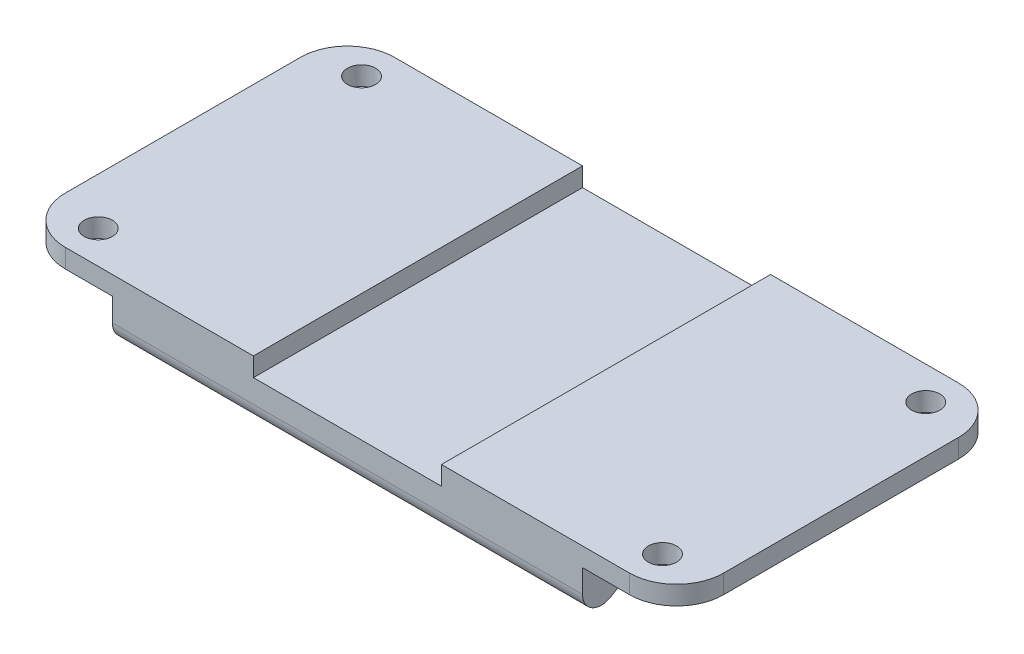
SolidWorks part; units mm, degrees
material "PEI"
ref_plane "Front Plane" through (0, 0, 0) normal (0, 0, 1) x (1, 0, 0)
ref_plane "Top Plane" through (0, 0, 0) normal (0, 1, 0) x (1, 0, 0)
ref_plane "Right Plane" through (0, 0, 0) normal (1, 0, 0) x (0, 0, -1)
sketch "Sketch1" plane through (0, 0, 0) normal (0, 1, 0) x (1, 0, 0)
  line L1 (25, -17.5) -> (-25, -17.5)
  line L2 (25, -17.5) -> (25, 17.5)
  line L3 (25, 17.5) -> (-25, 17.5)
  line L4 (-25, -17.5) -> (-25, 17.5)
  line L5 (25, -17.5) -> (-25, 17.5) construction
  line L6 (25, 17.5) -> (-25, -17.5) construction
  point P0 (0, 0)
  dimension "D1" = 35
  dimension "D2" = 50
extrude "Boss-Extrude1" add sketch "Sketch1" against normal blind 8
sketch "Sketch2" plane through (25, 0, 0) normal (1, 0, 0) x (0, 0, -1)
  line L0 (-17.5, -8) -> (-12.5, -5)
  line L1 (-12.5, -5) -> (12.5, -5)
  line L2 (0, -5) -> (0, -8)
  line L3 (17.5, -8) -> (12.5, -5)
  line L4 (17.5, 0) -> (-17.5, 0)
  line L5 (-17.5, 0) -> (-17.5, -8)
  line L6 (-17.5, -8) -> (17.5, -8)
  line L7 (17.5, -8) -> (17.5, 0)
  line L8 (17.5, 0) -> (-17.5, 0)
  line L9 (-17.5, 0) -> (-17.5, -8)
  line L10 (-17.5, -8) -> (17.5, -8)
  line L11 (17.5, -8) -> (17.5, 0)
  line M7 (-17.5, -8) -> (17.5, -8)
  dimension "D2" = 5
  dimension "D3" = 3
  dimension "D1" = 0
extrude "Cut-Extrude1" cut sketch "Sketch2" against normal through all and the other way through all contours L2 L1 L0 M7 | L3 L1 L2 M7
fillet "Fillet1" radius 2 4 edges at (0, -5, 12.5) (0, -5, -12.5) (0, -8, -17.5) (0, -8, 17.5)
sketch "Sketch3" plane through (0, 0, 17.5) normal (0, 0, 1) x (1, 0, 0)
  line L0 (-25, 0) -> (25, 0) construction
  line L1 (-10, 2) -> (10, 2)
  line L2 (-10, 2) -> (-10, -2)
  line L3 (-10, -2) -> (10, -2)
  line L4 (-25, 0) -> (-25, -4.4676)
  line L5 (-25, -4.4676) -> (25, -4.4676)
  line L6 (25, -4.4676) -> (25, 0)
  line L7 (25, 0) -> (-25, 0)
  line L8 (-25, 0) -> (-25, -4.4676)
  line L9 (-25, -4.4676) -> (25, -4.4676)
  line L10 (25, -4.4676) -> (25, 0)
  line L11 (25, 0) -> (-25, 0)
  line L12 (10, 2) -> (10, -2)
  line L13 (-10, 2) -> (10, -2) construction
  line L14 (-10, -2) -> (10, 2) construction
  line L15 (0, 0) -> (0, -4.4676)
  point P2 (0, 0)
  point P18 (0, 0)
  line M10 (25, 0) -> (-25, 0)
  dimension "D2" = 20
  dimension "D3" = 4
  dimension "D1" = 0
sketch "Sketch5" plane through (-25, 0, 0) normal (-1, 0, 0) x (0, 0, 1)
  line L1 (-17.5, 0) -> (17.5, 0)
  line L2 (-17.5, 0) -> (-17.5, -2)
  line L3 (-17.5, -2) -> (17.5, -2)
  line L4 (17.5, 0) -> (17.5, -2)
  line L6 (-17.5, 0) -> (-17.5, -4.4676)
  line L7 (-14.471, -6.1826) -> (-12.975, -5.285)
  line L8 (-11.946, -5) -> (11.946, -5)
  line L9 (12.975, -5.285) -> (14.471, -6.1826)
  line L10 (17.5, -4.4676) -> (17.5, 0)
  line L11 (17.5, 0) -> (-17.5, 0)
  line L12 (-17.5, 0) -> (-17.5, -4.4676)
  line L13 (-14.471, -6.1826) -> (-12.975, -5.285)
  line L14 (-11.946, -5) -> (11.946, -5)
  line L15 (12.975, -5.285) -> (14.471, -6.1826)
  line L16 (17.5, -4.4676) -> (17.5, 0)
  line L17 (17.5, 0) -> (-17.5, 0)
  arc A4 (-17.5, -4.4676) -> (-14.471, -6.1826) centre (-15.5, -4.4676) ccw
  arc A5 (-11.946, -5) -> (-12.975, -5.285) centre (-11.946, -7) ccw
  arc A6 (12.975, -5.285) -> (11.946, -5) centre (11.946, -7) ccw
  arc A7 (14.471, -6.1826) -> (17.5, -4.4676) centre (15.5, -4.4676) ccw
  arc A8 (-17.5, -4.4676) -> (-14.471, -6.1826) centre (-15.5, -4.4676) ccw
  arc A9 (-11.946, -5) -> (-12.975, -5.285) centre (-11.946, -7) ccw
  arc A10 (12.975, -5.285) -> (11.946, -5) centre (11.946, -7) ccw
  arc A11 (14.471, -6.1826) -> (17.5, -4.4676) centre (15.5, -4.4676) ccw
  line M13 (-17.5, 0) -> (-17.5, -4.4676)
  line M21 (17.5, -4.4676) -> (17.5, 0)
  line M22 (17.5, 0) -> (-17.5, 0)
  dimension "D2" = 2
  dimension "D1" = 0
extrude "Boss-Extrude2" add sketch "Sketch5" along normal blind 10 contours L3 M13 M21 M22
mirror "Mirror1" about plane through (0, 0, 0) normal (1, 0, 0) of "Boss-Extrude2"
sketch "Sketch6" plane through (0, 0, 0) normal (0, 1, 0) x (1, 0, 0)
  line L0 (0, 0) -> (-30, 0)
  line L1 (-30, 0) -> (-30, 14)
  line L2 (0, 0) -> (0, 17.5)
  line L4 (35, 17.5) -> (-35, 17.5)
  line L5 (-35, 17.5) -> (-35, -17.5)
  line L6 (-35, -17.5) -> (35, -17.5)
  line L7 (35, -17.5) -> (35, 17.5)
  line L8 (35, 17.5) -> (-35, 17.5)
  line L9 (-35, 17.5) -> (-35, -17.5)
  line L10 (-35, -17.5) -> (35, -17.5)
  line L11 (35, -17.5) -> (35, 17.5)
  circle A0 centre (-30, 14) radius 1.5
  circle A1 centre (-30, -14) radius 1.5
  circle A2 centre (30, -14) radius 1.5
  circle A3 centre (30, 14) radius 1.5
  dimension "D4" = 3
  dimension "D2" = 14
  dimension "D3" = 30
  dimension "D1" = 0
extrude "Cut-Extrude2" cut sketch "Sketch6" against normal blind 10
extrude "Cut-Extrude3" cut sketch "Sketch3" against normal through all contours L11 L15 L3 L12 | L15 L2 L3 M10
fillet "Fillet3" radius 5 4 edges at (35, -1, -17.5) (35, -1, 17.5) (-35, -1, -17.5) (-35, -1, 17.5)
